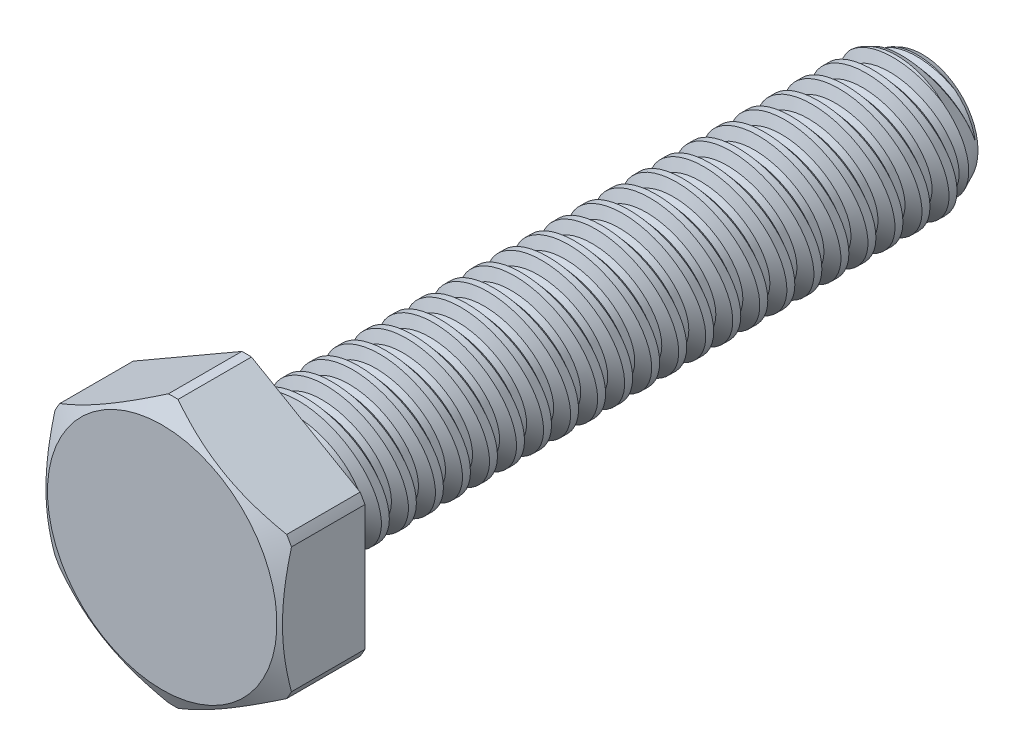
SolidWorks part; units mm, degrees
ref_plane "Front" through (0, 0, 0) normal (0, 0, 1) x (1, 0, 0)
ref_plane "Top" through (0, 0, 0) normal (0, 1, 0) x (1, 0, 0)
ref_plane "Right" through (0, 0, 0) normal (1, 0, 0) x (0, 0, -1)
sketch "Sketch1" plane through (0, 0, 0) normal (1, 0, 0) x (0, 0, -1)
  line L0 (-15.875, 0) -> (-19.8437, 0) construction
  line L1 (-15.875, 0) -> (-15.875, 5.5563) construction
  line L2 (-15.875, 0) -> (-19.8437, 0) construction
  line L3 (-15.875, -3.175) -> (15.875, -3.175) construction
  line L4 (-15.875, 0) -> (15.875, 0)
  line L5 (-15.875, 0) -> (-15.875, 3.175)
  line L6 (-15.875, 3.175) -> (15.875, 3.175)
  line L7 (15.875, 0) -> (15.875, 3.175)
  dimension "Screw Dia" = 6.35
  dimension "Screw Length" = 31.75
  dimension "Head Height" = 3.9688
  dimension "Head Width" = 11.1125
revolve "Revolve1" add sketch "Sketch1" angle 360 about L0
sketch "Sketch2" plane through (0, 0, 0) normal (1, 0, 0) x (0, 0, -1)
  line L0 (-15.875, 3.175) -> (-15.875, -3.175) construction
  line L1 (-15.875, -3.175) -> (-14.605, -3.175) construction
  line L2 (-14.605, -3.175) -> (-15.875, 3.175) construction
  line L3 (-15.875, 3.175) -> (-15.7193, 3.2061) construction
  line L4 (-14.6297, 3.4241) -> (-15.7193, 3.2061)
  line L5 (-15.7193, 3.2061) -> (-15.1954, 2.6099)
  line L6 (-15.1954, 2.6099) -> (-14.884, 2.6722)
  line L7 (-14.884, 2.6722) -> (-14.6297, 3.4241)
  line L8 (-15.0397, 2.641) -> (-15.1745, 3.3151) construction
  line L9 (-15.875, 0) -> (-15.875, 3.175) construction
  line L10 (-15.875, 3.175) -> (-15.1465, 3.175) construction
  line L11 (-15.1465, 3.175) -> (-13.8765, -3.175) construction
  line L12 (-13.8765, -3.175) -> (-14.605, -3.175) construction
  line L13 (-15.875, -3.175) -> (15.875, -3.175) construction
  line L14 (-15.875, -0.2727) -> (-13.148, 0.2727) construction
  line L15 (-15.875, 3.175) -> (15.875, 3.175) construction
  point P17 (-14.5115, 0)
  dimension "D1" = 1.27
  dimension "Thread Pitch" = 1.27
  dimension "D3" = 0.3175
  dimension "D4" = 0.1588
  dimension "D5" = 60
revolve "Cut-Revolve1" cut sketch "Sketch2" angle 360 about L14
sketch "Sketch3" plane through (0, 0, 0) normal (1, 0, 0) x (0, 0, -1)
  line L0 (14.6632, 3.175) -> (15.875, 2.6099)
  line L1 (15.875, 2.6099) -> (15.875, 3.175)
  line L2 (15.875, 3.175) -> (14.6632, 3.175)
  line L3 (-15.875, 3.175) -> (15.875, 3.175) construction
  line L4 (15.875, 0) -> (15.875, 3.175) construction
  line L5 (-15.1954, 2.6099) -> (15.875, 2.6099) construction
  line L6 (14.6632, 3.175) -> (14.6632, -3.175) construction
  line L7 (-15.875, -3.175) -> (15.875, -3.175) construction
  line L8 (0, 0) -> (14.6632, 0) construction
  dimension "D1" = 25
  dimension "D2" = 6.35
revolve "Cut-Revolve2" cut sketch "Sketch3" angle 360 about L8
pattern_linear "LPattern1" count 2 spacing 1.27 along (0, 0, 1) count 25 spacing 1.27 along (0, 0, 1)
sketch "Sketch5" plane through (0, 0, 15.875) normal (0, 0, 1) x (1, 0, 0)
  line L1 (0, 6.4158) -> (-5.5563, 3.2079)
  line L2 (-5.5563, 3.2079) -> (-5.5563, -3.2079)
  line L3 (-5.5563, -3.2079) -> (0, -6.4158)
  line L4 (0, -6.4158) -> (5.5562, -3.2079)
  line L5 (5.5562, -3.2079) -> (5.5562, 3.2079)
  line L6 (5.5562, 3.2079) -> (0, 6.4158)
  circle A0 centre (0, 0) radius 5.5563 construction
  dimension "D1" = 11.1125
extrude "Extrude1" add sketch "Sketch5" along normal up to vertex
sketch "Sketch6" plane through (0, 0, 0) normal (1, 0, 0) x (0, 0, -1)
  line L0 (-19.8437, 5.3896) -> (-19.3246, 6.2888)
  line L1 (-19.3246, 6.2888) -> (-15.875, 6.2888)
  line L2 (-15.875, 6.2888) -> (-15.875, 6.7968)
  line L3 (-15.875, 6.7968) -> (-19.8437, 6.7968)
  line L4 (-19.8437, 6.7968) -> (-19.8437, 5.3896)
  line L5 (-19.8437, 3.2079) -> (-19.8437, 6.4158) construction
  line L6 (-19.8437, 6.4158) -> (-15.875, 6.4158) construction
  line L7 (-15.875, 3.2079) -> (-15.875, 6.4158) construction
  line L8 (0, 0) -> (-19.3246, 0) construction
  line L9 (-15.875, 0) -> (-19.8437, 0) construction
  line L10 (-19.3246, 0) -> (-19.3246, 6.2888) construction
  line L11 (-17.8594, 6.7968) -> (-17.8594, 0) construction
  dimension "D1" = 30
  dimension "D2" = 0.127
  dimension "D3" = 0.508
  dimension "D4" = 10.7791
  dimension "D5" = 3.9687
  dimension "D6" = 31.75
revolve "Cut-Revolve3" cut sketch "Sketch6" angle 360 about L8
equation "\"D3@Sketch2\"=\"Thread Pitch@Sketch2\"/4"
equation "\"D4@Sketch2\"=\"Thread Pitch@Sketch2\"/8"
equation "\"D1@Sketch2\"=\"Thread Pitch@Sketch2\""
equation "\"D3@LPattern1\"=\"Thread Pitch@Sketch2\""
equation "\"D4@LPattern1\"=\"Thread Pitch@Sketch2\""
equation "\"D4@Sketch6\"=\"Head Width@Sketch1\"*.97"
equation "\"D2@LPattern1\"=\"Screw Length@Sketch1\"/\"Thread Pitch@Sketch2\""
